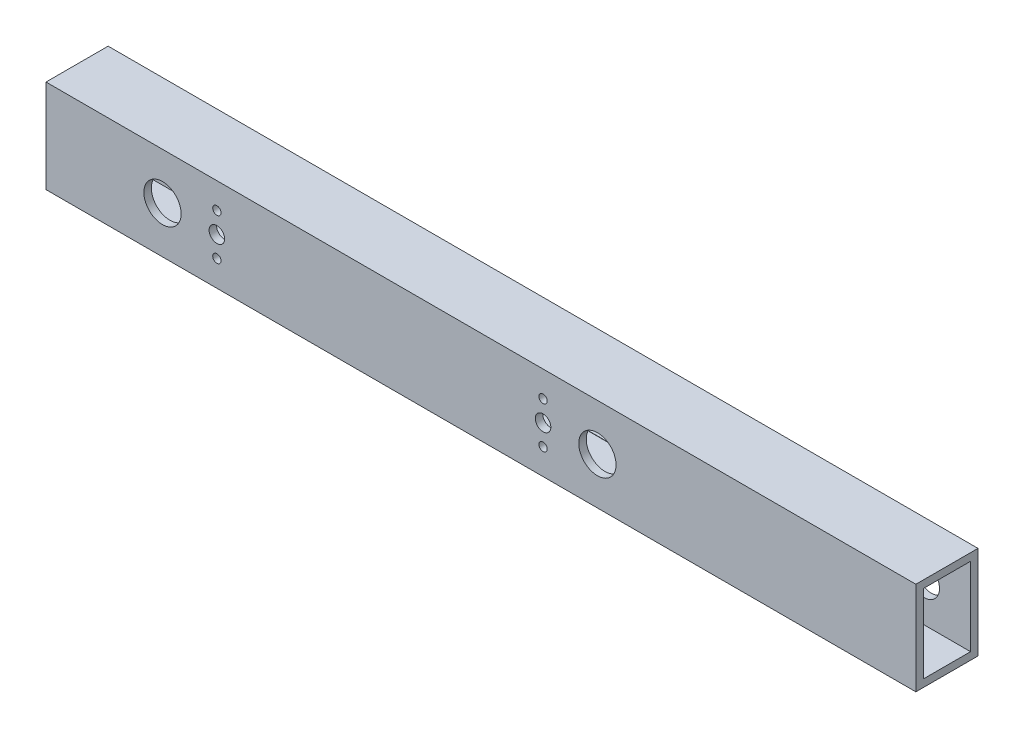
SolidWorks part; units mm, degrees
material "6061 Alloy"
ref_plane "Front Plane" through (0, 0, 0) normal (0, 0, 1) x (1, 0, 0)
ref_plane "Top Plane" through (0, 0, 0) normal (0, 1, 0) x (1, 0, 0)
ref_plane "Right Plane" through (0, 0, 0) normal (1, 0, 0) x (0, 0, -1)
sketch "Sketch1" plane through (0, 0, 0) normal (1, 0, 0) x (0, 0, -1)
  line L0 (-9.652, 16.002) -> (9.652, 16.002)
  line L1 (-12.7, -19.05) -> (12.7, -19.05)
  line L2 (-12.7, -19.05) -> (-12.7, 19.05)
  line L3 (-12.7, 19.05) -> (12.7, 19.05)
  line L4 (12.7, -19.05) -> (12.7, 19.05)
  line L5 (-12.7, -19.05) -> (12.7, 19.05) construction
  line L6 (-12.7, 19.05) -> (12.7, -19.05) construction
  line L7 (9.652, -16.002) -> (9.652, 16.002)
  line L8 (-9.652, -16.002) -> (9.652, -16.002)
  line L9 (-9.652, -16.002) -> (-9.652, 16.002)
  point P0 (0, 0)
  dimension "D1" = 25.4
  dimension "D2" = 38.1
  dimension "D3" = 3.048
extrude "Boss-Extrude1" add sketch "Sketch1" along normal blind 355.6
sketch "Sketch2" plane through (0, 0, -12.7) normal (0, 0, -1) x (-1, 0, 0)
  line L0 (-355.6, 0) -> (0, 0) construction
  line L1 (-355.6, -19.05) -> (-355.6, 19.05) construction
  circle A0 centre (-336.55, 0) radius 6.35
  dimension "D2" = 12.7
  dimension "D1" = 19.05
extrude "Cut-Extrude1" cut sketch "Sketch2" against normal up to next
sketch "Sketch3" [suppressed] plane through (0, 0, -12.7) normal (0, 0, -1) x (-1, 0, 0)
  line L0 (0, 0) -> (-355.6, 0) construction
  line L1 (-355.6, -19.05) -> (-355.6, 19.05) construction
  circle A0 centre (-273.05, 0) radius 3.175
  circle A1 centre (-336.55, 0) radius 6.35 construction
  dimension "D1" = 63.5
  dimension "D2" = 6.35
extrude "Cut-Extrude2" [suppressed] cut sketch "Sketch3" against normal up to next
sketch "Sketch4" [suppressed] plane through (0, 0, 12.7) normal (0, 0, 1) x (1, 0, 0)
  line L0 (0, 0) -> (355.6, 0) construction
  line L1 (260.35, -12.7) -> (285.75, -12.7)
  line L2 (254, -6.35) -> (254, 6.35)
  line L3 (260.35, 12.7) -> (285.75, 12.7)
  line L4 (292.1, -6.35) -> (292.1, 6.35)
  line L5 (254, -12.7) -> (292.1, 12.7) construction
  line L6 (254, 12.7) -> (292.1, -12.7) construction
  line L7 (355.6, 19.05) -> (355.6, -19.05) construction
  arc A0 (285.75, 12.7) -> (292.1, 6.35) centre (285.75, 6.35) cw
  arc A1 (285.75, -12.7) -> (292.1, -6.35) centre (285.75, -6.35) ccw
  arc A2 (260.35, -12.7) -> (254, -6.35) centre (260.35, -6.35) cw
  arc A3 (254, 6.35) -> (260.35, 12.7) centre (260.35, 6.35) cw
  point P0 (273.05, 0)
  dimension "D4" = 6.35
  dimension "D1" = 38.1
  dimension "D2" = 25.4
  dimension "D3" = 63.5
extrude "Cut-Extrude3" [suppressed] cut sketch "Sketch4" against normal up to next
sketch "Sketch5" plane through (0, 0, 12.7) normal (0, 0, 1) x (1, 0, 0)
  line L0 (47.625, 19.05) -> (47.625, -19.05) construction
  line L1 (355.6, 19.05) -> (0, 19.05) construction
  line L2 (355.6, -19.05) -> (0, -19.05) construction
  line L3 (31.75, 0) -> (63.5, 0) construction
  line L4 (0, 19.05) -> (0, -19.05) construction
  line L5 (225.425, 19.05) -> (225.425, -19.05) construction
  line L6 (209.55, 0) -> (241.3, 0) construction
  circle A0 centre (47.625, 0) radius 7.62
  circle A1 centre (225.425, 0) radius 7.62
  point P8 (47.625, 0)
  point P18 (225.425, 0)
  dimension "D2" = 15.24
  dimension "D6" = 15.24
  dimension "D1" = 47.625
  dimension "D3" = 31.75
  dimension "D4" = 225.425
  dimension "D5" = 31.75
extrude "Cut-Extrude4" cut sketch "Sketch5" against normal up to next
sketch "Sketch6" plane through (0, 0, 12.7) normal (0, 0, 1) x (1, 0, 0)
  line L0 (47.625, 0) -> (225.425, 0) construction
  line L1 (69.85, 0) -> (69.85, 8.5) construction
  line L2 (203.2, 8.5) -> (203.2, -8.5) construction
  line L3 (69.85, 0) -> (69.85, -8.5) construction
  circle A0 centre (69.85, 0) radius 3.175
  circle A1 centre (203.2, 0) radius 3.175
  dimension "D2" = 6.35
  dimension "D5" = 6.35
  dimension "D3" = 22.225
  dimension "D1" = 17
  dimension "D4" = 17
  dimension "D6" = 22.225
extrude "Cut-Extrude5" cut sketch "Sketch6" against normal up to next
sketch "Sketch7" plane through (0, 0, -12.7) normal (0, 0, -1) x (-1, 0, 0)
  line L0 (0, 0) -> (-355.6, 0) construction
  line L1 (-242.8875, -15.875) -> (-185.7375, -15.875)
  line L2 (-246.0625, -12.7) -> (-246.0625, 12.7)
  line L3 (-242.8875, 15.875) -> (-185.7375, 15.875)
  line L4 (-182.5625, -12.7) -> (-182.5625, 12.7)
  line L5 (-246.0625, -15.875) -> (-182.5625, 15.875) construction
  line L6 (-246.0625, 15.875) -> (-182.5625, -15.875) construction
  line L7 (-87.3125, -15.875) -> (-30.1625, -15.875)
  line L8 (-90.4875, -12.7) -> (-90.4875, 12.7)
  line L9 (-87.3125, 15.875) -> (-30.1625, 15.875)
  line L10 (-26.9875, -12.7) -> (-26.9875, 12.7)
  line L11 (-90.4875, -15.875) -> (-26.9875, 15.875) construction
  line L12 (-90.4875, 15.875) -> (-26.9875, -15.875) construction
  line L13 (-355.6, -19.05) -> (-355.6, 19.05) construction
  line L14 (-214.3125, 0) -> (-214.3125, 15.875) construction
  line L15 (-58.7375, 0) -> (-58.7375, 15.875) construction
  circle A0 centre (-69.85, 0) radius 3.175 construction
  circle A1 centre (-47.625, 0) radius 7.62 construction
  circle A2 centre (-203.2, 0) radius 3.175 construction
  circle A3 centre (-225.425, 0) radius 7.62 construction
  circle A4 centre (-69.85, 0) radius 3.175 construction
  circle A5 centre (-47.625, 0) radius 7.62 construction
  circle A6 centre (-203.2, 0) radius 3.175 construction
  circle A7 centre (-225.425, 0) radius 7.62 construction
  arc A8 (-26.9875, -12.7) -> (-30.1625, -15.875) centre (-30.1625, -12.7) cw
  arc A9 (-87.3125, -15.875) -> (-90.4875, -12.7) centre (-87.3125, -12.7) cw
  arc A10 (-26.9875, 12.7) -> (-30.1625, 15.875) centre (-30.1625, 12.7) ccw
  arc A11 (-87.3125, 15.875) -> (-90.4875, 12.7) centre (-87.3125, 12.7) ccw
  arc A12 (-246.0625, -12.7) -> (-242.8875, -15.875) centre (-242.8875, -12.7) ccw
  arc A13 (-185.7375, -15.875) -> (-182.5625, -12.7) centre (-185.7375, -12.7) ccw
  arc A14 (-182.5625, 12.7) -> (-185.7375, 15.875) centre (-185.7375, 12.7) ccw
  arc A15 (-242.8875, 15.875) -> (-246.0625, 12.7) centre (-242.8875, 12.7) ccw
  point P0 (-214.3125, 0)
  point P5 (-58.7375, 0)
  dimension "D4" = 3.175
  dimension "D1" = 31.75
  dimension "D2" = 63.5
  dimension "D3" = 63.5
extrude "Cut-Extrude6" cut sketch "Sketch7" against normal up to next
sketch "Sketch8" plane through (0, 0, -12.7) normal (0, 0, -1) x (-1, 0, 0)
  line L0 (-182.5625, 3.175) -> (-90.4875, 3.175) construction
  line L3 (-165.1, 19.05) -> (-165.1, -19.05) construction
  line L4 (-355.6, 19.05) -> (0, 19.05) construction
  line L5 (-355.6, -19.05) -> (0, -19.05) construction
  line L6 (-107.95, 19.05) -> (-107.95, -19.05) construction
  line L7 (-136.525, 3.175) -> (-136.525, 19.05) construction
  line L8 (-90.4875, 12.7) -> (-90.4875, -12.7) construction
  line L9 (-182.5625, -12.7) -> (-182.5625, 12.7) construction
  point P2 (-107.95, 3.175)
  point P19 (-165.1, 3.175)
  dimension "D1" = 57.15
  dimension "D2" = 22.225
hole_wizard "M3 Clearance Hole1" positions "3DSketch1" profile "Sketch9" hole size "M3" standard "ANSI Metric" end condition up to next
sketch3d "3DSketch1"
  point P13 (165.1, 3.175, -12.7)
  point P16 (107.95, 3.175, -12.7)
sketch "Sketch9" plane through (165.1, 3.175, -12.7) normal (1, 0, 0) x (0, 1, 0)
  line L0 (0, 0) -> (0, 3.048)
  line L1 (0, 3.048) -> (1.7, 3.048)
  line L2 (1.7, 3.048) -> (1.7, 0)
  line L5 (1.7, 0) -> (0, 0)
  line L11 (0, -6.35) -> (0, 107.95) construction
  dimension "Thru Hole Dia." = 3.4
  dimension "Thru Hole Depth" = 3.048
hole_wizard "M3 Clearance Hole2" positions "3DSketch2" profile "Sketch10" hole size "M3" standard "ANSI Metric" end condition up to next
sketch3d "3DSketch2"
  point P0 (69.85, 8.5, 12.7)
  point P3 (69.85, -8.5, 12.7)
  point P6 (203.2, 8.5, 12.7)
  point P9 (203.2, -8.5, 12.7)
sketch "Sketch10" plane through (69.85, 8.5, 12.7) normal (1, 0, 0) x (0, -1, 0)
  line L0 (0, 0) -> (0, 3.048)
  line L1 (0, 3.048) -> (1.7, 3.048)
  line L2 (1.7, 3.048) -> (1.7, 0)
  line L5 (1.7, 0) -> (0, 0)
  line L11 (0, -6.35) -> (0, 107.95) construction
  dimension "Thru Hole Dia." = 3.4
  dimension "Thru Hole Depth" = 3.048
sketch "Sketch11" [suppressed] plane through (0, 0, -12.7) normal (0, 0, -1) x (-1, 0, 0)
  line L0 (-273.05, 8.5) -> (-273.05, -8.5) construction
  circle A0 centre (-273.05, 0) radius 3.175 construction
  point P2 (-273.05, 0)
  dimension "D1" = 17
hole_wizard "M3 Clearance Hole3" [suppressed] positions "3DSketch3" profile "Sketch12" hole size "M3" standard "ANSI Metric"
sketch3d "3DSketch3"
  point P0 (273.05, 8.5, -12.7)
  point P3 (273.05, -8.5, -12.7)
sketch "Sketch12" plane through (273.05, 8.5, -12.7) normal (1, 0, 0) x (0, 1, 0)
  line L0 (0, 0) -> (0, 25.4)
  line L1 (0, 25.4) -> (1.7, 25.4)
  line L2 (1.7, 25.4) -> (1.7, 0)
  line L5 (1.7, 0) -> (0, 0)
  line L11 (0, -6.35) -> (0, 107.95) construction
  dimension "Thru Hole Dia." = 3.4
  dimension "Thru Hole Depth" = 25.4
equation "\"D5@Sketch5\"=\"D3@Sketch5\""
equation "\"D6@Sketch5\"=\"D2@Sketch5\""
equation "\"D4@Sketch6\"=\"D1@Sketch6\""
equation "\"D5@Sketch6\"=\"D2@Sketch6\""
equation "\"D6@Sketch6\"=\"D3@Sketch6\""
equation "\"D3@Sketch7\"=\"D2@Sketch7\""
